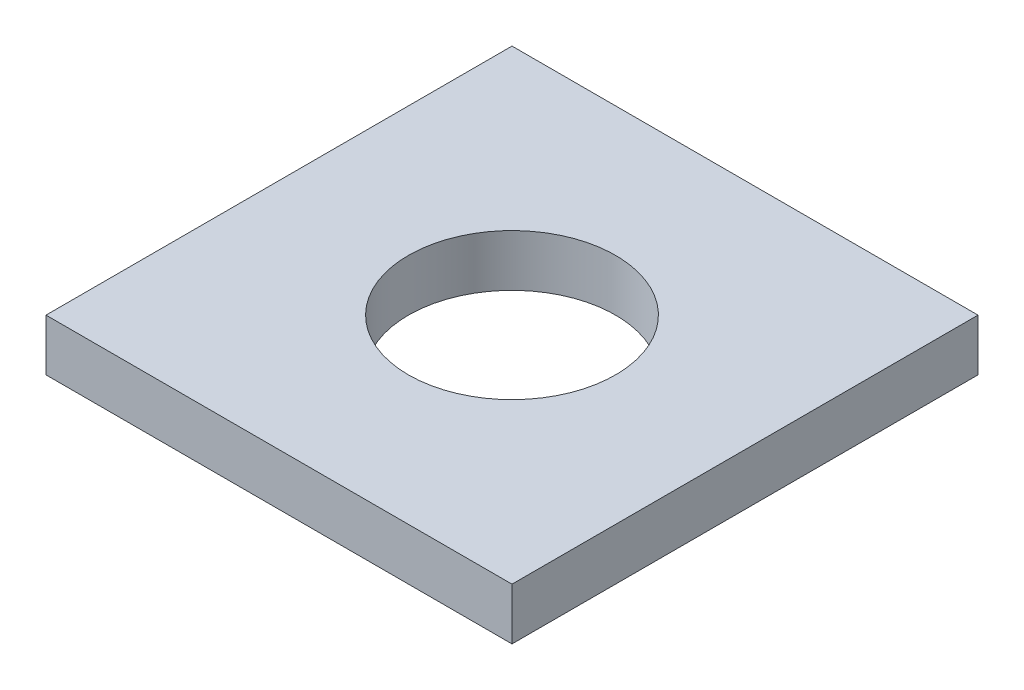
SolidWorks part; units mm, degrees
ref_plane "Front Plane" through (0, 0, 0) normal (0, 0, 1) x (1, 0, 0)
ref_plane "Top Plane" through (0, 0, 0) normal (0, 1, 0) x (1, 0, 0)
ref_plane "Right Plane" through (0, 0, 0) normal (1, 0, 0) x (0, 0, -1)
sketch "Sketch1" plane through (0, 0, 0) normal (0, 1, 0) x (1, 0, 0)
  line L1 (-22.5, -22.5) -> (22.5, -22.5)
  line L2 (-22.5, -22.5) -> (-22.5, 22.5)
  line L3 (-22.5, 22.5) -> (22.5, 22.5)
  line L4 (22.5, -22.5) -> (22.5, 22.5)
  line L5 (-22.5, -22.5) -> (22.5, 22.5) construction
  line L6 (-22.5, 22.5) -> (22.5, -22.5) construction
  circle A0 centre (0, 0) radius 10
  point P0 (0, 0)
  dimension "D2" = 20
  dimension "D1" = 45
extrude "Boss-Extrude1" add sketch "Sketch1" along normal blind 5
